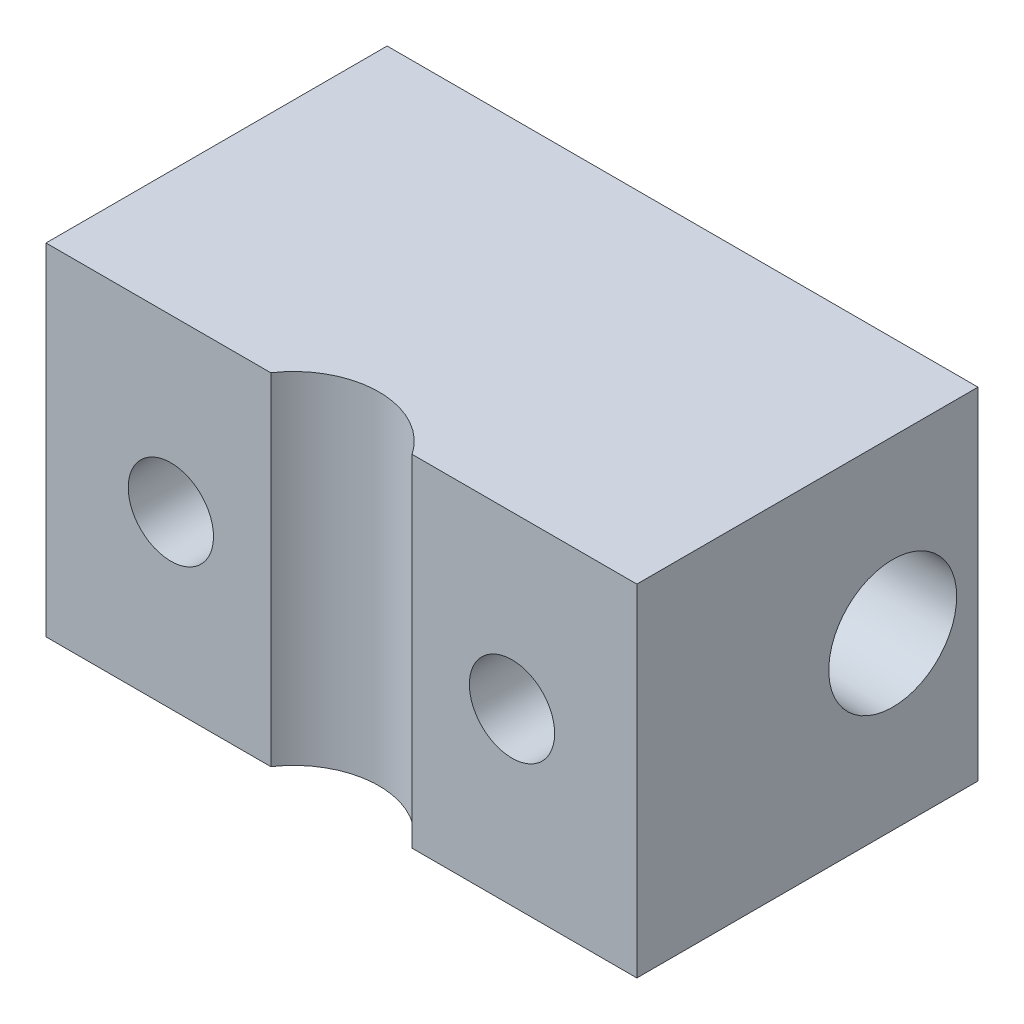
SolidWorks part; units mm, degrees
ref_plane "Front Plane" through (0, 0, 0) normal (0, 0, 1) x (1, 0, 0)
ref_plane "Top Plane" through (0, 0, 0) normal (0, 1, 0) x (1, 0, 0)
ref_plane "Right Plane" through (0, 0, 0) normal (1, 0, 0) x (0, 0, -1)
sketch "Sketch1" plane through (0, 0, 0) normal (0, 1, 0) x (1, 0, 0)
  line L0 (6.8143, 0) -> (10.9982, 0)
  line L1 (0, 0) -> (4.1839, 0)
  line L2 (0, 0) -> (0, 6.35)
  line L3 (0, 6.35) -> (10.9982, 6.35)
  line L4 (10.9982, 0) -> (10.9982, 6.35)
  arc A0 (6.8143, 0) -> (4.1839, 0) centre (5.4991, -0.889) ccw
  point P6 (0, 0)
  point P7 (3.775, 0)
  point P8 (0, 0)
  dimension "D3" = 1.5875
  dimension "D1" = 10.9982
  dimension "D2" = 0.889
  dimension "D4" = 6.35
extrude "Boss-Extrude1" add sketch "Sketch1" along normal blind 6.35
hole_wizard "1/16 (0.0625) Diameter Hole1" positions "Sketch3" profile "Sketch4" hole size "1/16" standard "ANSI Inch"
sketch "Sketch3" plane through (0, 0, 0) normal (0, 0, 1) x (1, 0, 0)
  line L7 (0, 0) -> (10.9982, 0)
  line L9 (5.4991, 0) -> (5.4991, -0.9893)
  line L11 (0, 3.175) -> (-0.9105, 3.175)
  line L12 (0, 6.35) -> (0, 0) construction
  point P0 (2.3241, 3.175)
  point P33 (8.6741, 3.175)
  point P39 (0, 0)
  dimension "D1" = 6.35
sketch "Sketch4" plane through (2.3241, 3.175, 0) normal (1, 0, 0) x (0, -1, 0)
  line L0 (0, 0) -> (0, 2.0644)
  line L1 (0, 2.0644) -> (0.7937, 1.5875)
  line L2 (0.7937, 1.5875) -> (0.7937, 0)
  line L5 (0.7937, 0) -> (0, 0)
  line L10 (0, 2.0644) -> (-0.7937, 1.5875) construction
  line L11 (0, -6.35) -> (0, 107.95) construction
  dimension "Hole Dia." = 1.5875
  dimension "Hole Depth" = 1.5875
  dimension "Drill Angle" = 118
hole_wizard "3/32 (0.09375) Diameter Hole1" positions "Sketch5" profile "Sketch7" hole size "3/32" standard "ANSI Inch" end condition through all
sketch "Sketch5" plane through (10.9982, 0, 0) normal (1, 0, 0) x (0, 0, -1)
  line L0 (0, 3.175) -> (-0.828, 3.175)
  line L1 (0, 6.35) -> (0, 0) construction
  point P0 (4.7625, 3.175)
  dimension "D1" = 4.7625
sketch "Sketch7" plane through (10.9982, 3.175, -4.7625) normal (0, 1, 0) x (0, 0, -1)
  line L0 (0, 0) -> (0, 10.9982)
  line L1 (0, 10.9982) -> (1.1906, 10.9982)
  line L2 (1.1906, 10.9982) -> (1.1906, 0)
  line L5 (1.1906, 0) -> (0, 0)
  line L11 (0, -6.35) -> (0, 107.95) construction
  dimension "Thru Hole Dia." = 2.3812
  dimension "Thru Hole Depth" = 10.9982
